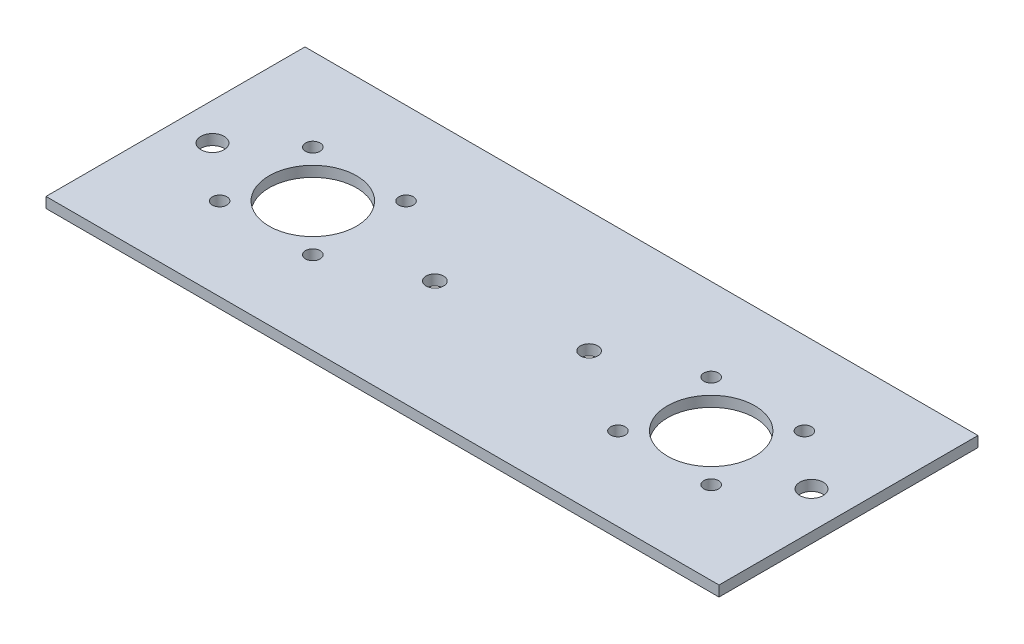
SolidWorks part; units mm, degrees
material "Acrylic (Medium-high impact)"
ref_plane "Front Plane" through (0, 0, 0) normal (0, 0, 1) x (1, 0, 0)
ref_plane "Top Plane" through (0, 0, 0) normal (0, 1, 0) x (1, 0, 0)
ref_plane "Right Plane" through (0, 0, 0) normal (1, 0, 0) x (0, 0, -1)
sketch "Sketch1" plane through (0, 0, 0) normal (0, 1, 0) x (1, 0, 0)
  line L0 (-231.05, 0) -> (-183.9, 0)
  line L1 (-231.05, 44.45) -> (0, 44.45)
  line L2 (-231.05, 44.45) -> (-231.05, -44.45)
  line L3 (-231.05, -44.45) -> (0, -44.45)
  line L4 (0, 44.45) -> (0, -44.45)
  line L5 (-115.525, -44.45) -> (-115.525, 44.45)
  line L7 (0, 0) -> (-47.15, 0)
  circle A0 centre (-183.9, 0) radius 15
  circle A1 centre (-47.15, 0) radius 15
  circle A2 centre (-63.15, -16) radius 2.5
  circle A3 centre (-31.15, -16) radius 2.5
  circle A4 centre (-31.15, 16) radius 2.5
  circle A5 centre (-63.15, 16) radius 2.5
  circle A6 centre (-167.9, 16) radius 2.5
  circle A7 centre (-199.9, 16) radius 2.5
  circle A8 centre (-199.9, -16) radius 2.5
  circle A9 centre (-167.9, -16) radius 2.5
  circle A10 centre (-139.15, -2.859) radius 3
  circle A11 centre (-91.9, 2.859) radius 3
  circle A12 centre (-218.35, 0) radius 4
  circle A13 centre (-12.7, 0) radius 4
  point P0 (0, 0)
  dimension "D5" = 30
  dimension "D6" = 30
  dimension "D1" = 88.9
  dimension "D2" = 231.05
  dimension "D3" = 47.15
  dimension "D4" = 47.15
extrude "Boss-Extrude1" add sketch "Sketch1" against normal blind 3.6 contours L2 L1 L4 L3 | A9 | A8 | A7 | A6 | A3 | A2 | A5 | A4 | A0 | A1 | A10 | A11 | A12 | A13
equation "\"3.6mmcm\"=1"
